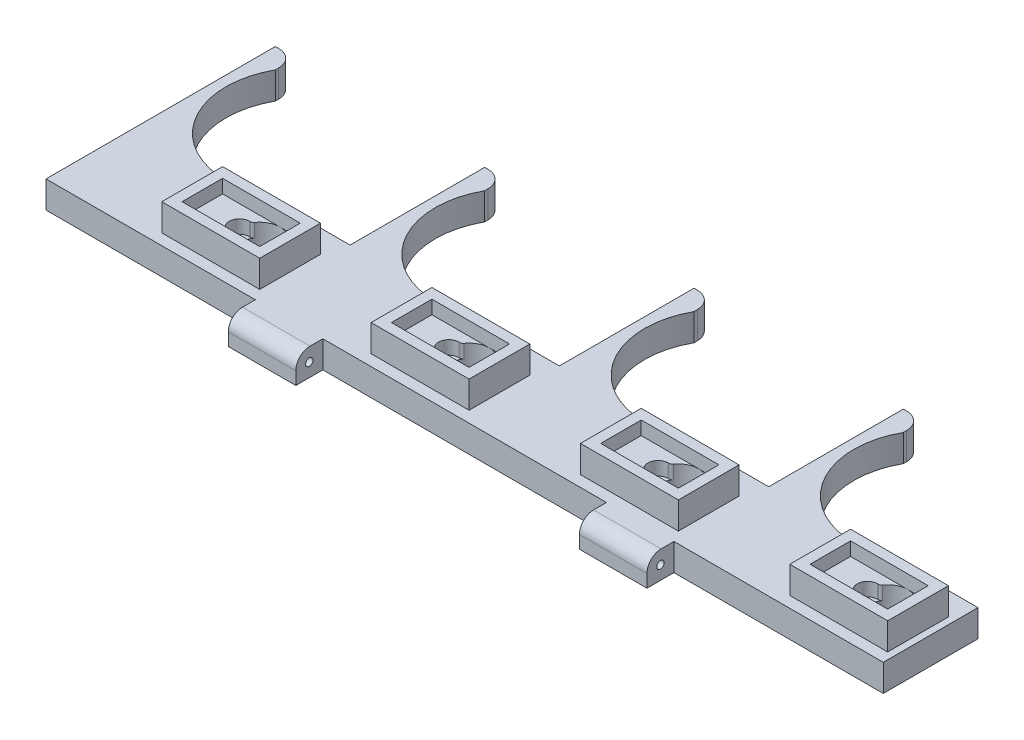
SolidWorks part; units mm, degrees
ref_plane "Plan de face" through (0, 0, 0) normal (0, 0, 1) x (1, 0, 0)
ref_plane "Plan de dessus" through (0, 0, 0) normal (0, 1, 0) x (1, 0, 0)
ref_plane "Plan de droite" through (0, 0, 0) normal (1, 0, 0) x (0, 0, -1)
sketch "Esquisse1" plane through (0, 0, 0) normal (0, 1, 0) x (1, 0, 0)
  line L1 (0, 0) -> (6, 0)
  line L2 (0, 0) -> (0, 67.9235)
  line L3 (0, 67.9235) -> (1, 67.9235)
  line L4 (6, 0) -> (6, 67.9235) construction
  line L5 (36, 0) -> (6, 0)
  line L6 (6, 61.9235) -> (6, 62.9235)
  line L7 (52, 50.3046) -> (52, 0) construction
  line L8 (36, 28.056) -> (62, 28.056)
  line L10 (36, 0) -> (62, 0)
  line L11 (62, 28.056) -> (62, 0)
  line L12 (36, 28.056) -> (36, 0) construction
  line L13 (52, 12.3046) -> (51, 12.3046) construction
  arc A0 (6, 61.9235) -> (36, 28.056) centre (27, 50.3046) ccw
  circle A1 centre (27, 50.3046) radius 25 construction
  arc A2 (1, 67.9235) -> (6, 62.9235) centre (1, 62.9235) cw
  circle A3 centre (51, 12.3046) radius 6
  dimension "D1" = 24
  dimension "D3" = 50
  dimension "D7" = 5
  dimension "D9" = 12
  dimension "D2" = 21
  dimension "D4" = 30
  dimension "D5" = 6
  dimension "D6" = 6
  dimension "D8" = 1
  dimension "D10" = 38
  dimension "D11" = 62
extrude "Boss.-Extru.1" add sketch "Esquisse1" along normal blind 8
sketch "Esquisse2" plane through (0, 8, 0) normal (0, 1, 0) x (1, 0, 0)
  line L0 (51, 12.3046) -> (45, 12.3046) construction
  line L1 (45, 15.3046) -> (45.2554, 15.3046)
  line L2 (45, 9.3046) -> (45.2554, 9.3046)
  line L8 (31, 21.3046) -> (60, 21.3046)
  line L9 (31, 21.3046) -> (31, 3.3046)
  line L10 (31, 3.3046) -> (60, 3.3046)
  line L11 (60, 21.3046) -> (60, 3.3046)
  circle A0 centre (51, 12.3046) radius 6 construction
  circle A1 centre (45, 12.3046) radius 3 construction
  arc A2 (46.0761, 15.7332) -> (46.0761, 8.876) centre (51, 12.3046) cw
  arc A3 (45, 15.3046) -> (45, 9.3046) centre (45, 12.3046) ccw
  arc A4 (45.2554, 9.3046) -> (46.0761, 8.876) centre (45.2554, 8.3046) cw
  arc A5 (45.2554, 15.3046) -> (46.0761, 15.7332) centre (45.2554, 16.3046) ccw
  point P15 (45.8038, 9.3046)
  point P18 (45.8038, 15.3046)
  point P27 (60, 12.3046)
  dimension "D1" = 12
  dimension "D2" = 6
  dimension "D4" = 1
  dimension "D3" = 6
  dimension "D5" = 9
  dimension "D7" = 18
  dimension "D8" = 29
extrude "Boss.-Extru.2" add sketch "Esquisse2" along normal blind 4 contours L9 L8 L11 L10 | A3 L2 A4 A2 A5 L1
sketch "Esquisse3" plane through (0, 12, 0) normal (0, 1, 0) x (1, 0, 0)
  line L1 (34, 18.3046) -> (57, 18.3046)
  line L2 (34, 18.3046) -> (34, 6.3046)
  line L3 (34, 6.3046) -> (57, 6.3046)
  line L4 (57, 18.3046) -> (57, 6.3046)
  line L5 (31, 21.3046) -> (60, 21.3046)
  line L6 (31, 21.3046) -> (31, 3.3046)
  line L7 (31, 3.3046) -> (60, 3.3046)
  line L8 (60, 21.3046) -> (60, 3.3046)
  arc A0 (46.0761, 8.876) -> (46.0761, 15.7332) centre (51, 12.3046) ccw construction
  dimension "D1" = 12
  dimension "D2" = 23
extrude "Boss.-Extru.3" add sketch "Esquisse3" along normal blind 4
sketch "Esquisse4" plane through (0, 0, 0) normal (0, -1, 0) x (1, 0, 0)
  line L0 (62, -28.056) -> (36, -28.056) construction
  line L1 (47.7, -17.056) -> (54.3, -17.056)
  line L3 (47.7, -28.056) -> (54.3, -28.056)
  line L5 (51, -12.3046) -> (51, -17.056) construction
  line L6 (51, -12.3046) -> (52.0099, -17.056) construction
  line L7 (55.1937, -16.1623) -> (57.7218, -28.056)
  line L8 (54.3, -17.056) -> (55.1937, -16.1623)
  line L9 (54.3, -28.056) -> (57.7218, -28.056)
  line L10 (54.3, -17.056) -> (54.3, -28.056) construction
  line L11 (46.8063, -16.1623) -> (44.2782, -28.056)
  line L12 (46.8063, -16.1623) -> (47.7, -17.056)
  line L13 (47.7, -17.056) -> (47.7, -28.056) construction
  line L14 (44.2782, -28.056) -> (47.7, -28.056)
  point P12 (51, -17.056)
  dimension "D1" = 12
  dimension "D2" = 3.3
  dimension "D3" = 6.6
  dimension "D4" = 11
  dimension "D5" = 135
extrude "Enlèv. mat.-Extru.1" cut sketch "Esquisse4" against normal blind 4
pattern_linear "Répétition linéaire1" count 4 spacing 62 along (1, 0, 0) of "Boss.-Extru.1", "Boss.-Extru.3", "Boss.-Extru.2", "Enlèv. mat.-Extru.1"
sketch "Esquisse5" plane through (62, 0, 0) normal (-1, 0, 0) x (0, 0, 1)
  line L0 (0, 8) -> (8, 0) construction
  line L1 (0, 8) -> (3.8, 8)
  line L2 (0, 8) -> (0, 0)
  line L3 (0, 0) -> (8, 0)
  line L4 (8, 3.8) -> (8, 0)
  circle A0 centre (4, 4) radius 1.1
  arc A1 (3.8, 8) -> (8, 3.8) centre (3.8, 3.8) cw
  point P9 (8, 8)
  dimension "D3" = 2.2
  dimension "D4" = 4.2
  dimension "D1" = 8
  dimension "D2" = 8
extrude "Boss.-Extru.4" add sketch "Esquisse5" against normal blind 20
mirror "Symétrie1" about plane through (124, 8, 0) normal (1, 0, 0) of "Boss.-Extru.4"
